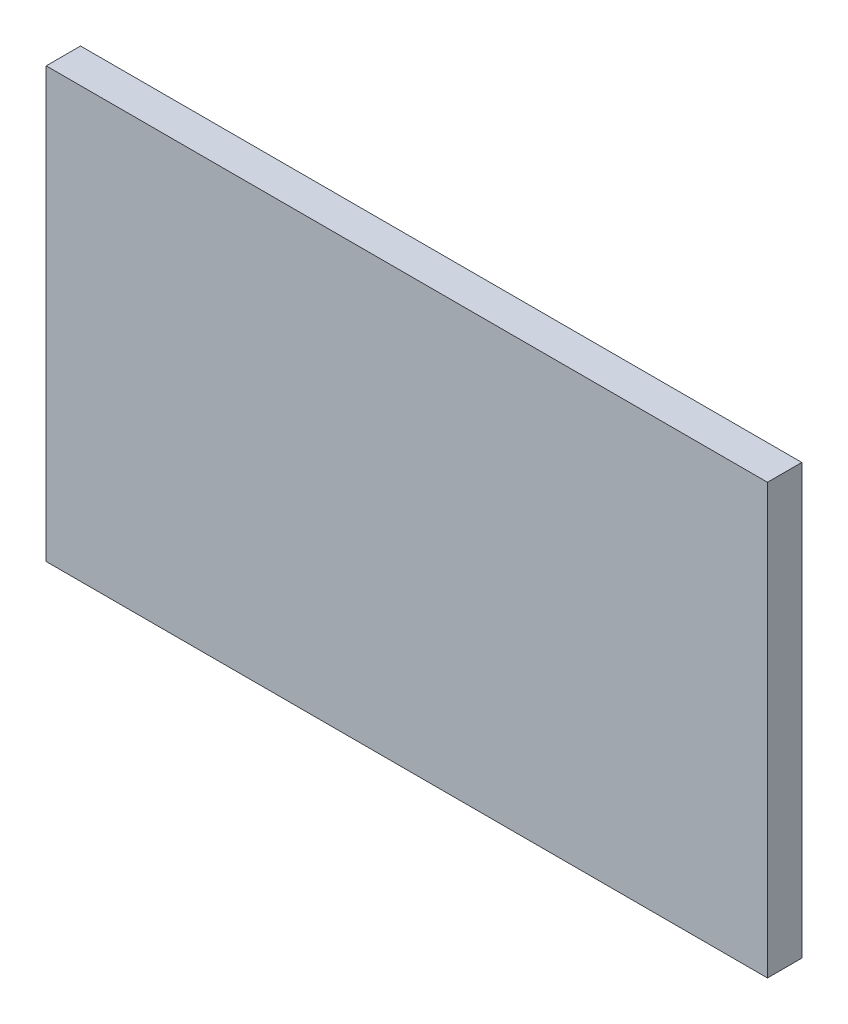
SolidWorks part; units mm, degrees
ref_plane "正面" through (0, 0, 0) normal (0, 0, 1) x (1, 0, 0)
ref_plane "平面" through (0, 0, 0) normal (0, 1, 0) x (1, 0, 0)
ref_plane "右側面" through (0, 0, 0) normal (1, 0, 0) x (0, 0, -1)
sketch "ｽｹｯﾁ1" plane through (0, 0, 0) normal (0, 0, 1) x (1, 0, 0)
  line L1 (0, 0) -> (420, 0)
  line L2 (0, 0) -> (0, 250)
  line L3 (0, 250) -> (420, 250)
  line L4 (420, 0) -> (420, 250)
  dimension "D1" = 250
  dimension "D2" = 420
extrude "ﾎﾞｽ - 押し出し1" add sketch "ｽｹｯﾁ1" along normal blind 20
